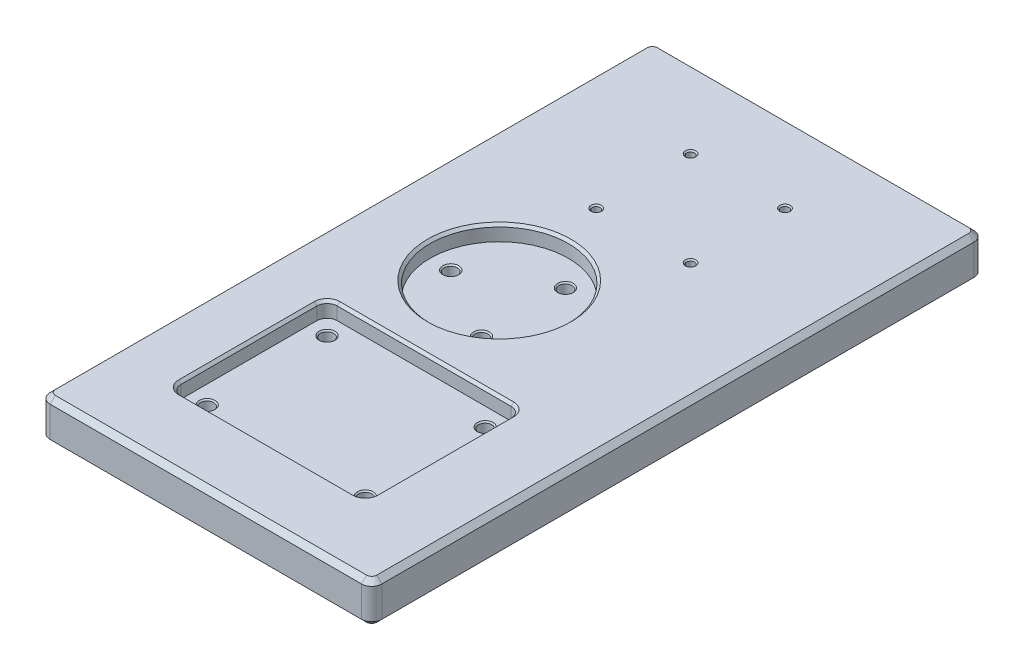
SolidWorks part; units mm, degrees
material "PET"
ref_plane "Front Plane" through (0, 0, 0) normal (0, 0, 1) x (1, 0, 0)
ref_plane "Top Plane" through (0, 0, 0) normal (0, 1, 0) x (1, 0, 0)
ref_plane "Right Plane" through (0, 0, 0) normal (1, 0, 0) x (0, 0, -1)
sketch "Sketch1" plane through (0, 0, 0) normal (0, 1, 0) x (1, 0, 0)
  line L1 (65, -120) -> (-65, -120)
  line L2 (65, -120) -> (65, 120)
  line L3 (65, 120) -> (-65, 120)
  line L4 (-65, -120) -> (-65, 120)
  line L5 (65, -120) -> (-65, 120) construction
  line L6 (65, 120) -> (-65, -120) construction
  point P0 (0, 0)
  dimension "D1" = 240
  dimension "D2" = 130
extrude "Boss-Extrude1" add sketch "Sketch1" along normal blind 16
sketch "Sketch7" plane through (0, 16, 0) normal (0, 1, 0) x (1, 0, 0)
  line L0 (-3, 0) -> (0, 0) construction
  line L1 (-41.1, -92.6) -> (35.1, -92.6)
  line L2 (-41.1, -92.6) -> (-41.1, -31.4)
  line L3 (-41.1, -31.4) -> (35.1, -31.4)
  line L4 (35.1, -92.6) -> (35.1, -31.4)
  line L5 (-41.1, -92.6) -> (35.1, -31.4) construction
  line L6 (-41.1, -31.4) -> (35.1, -92.6) construction
  line L7 (-3, 0) -> (-3, -62) construction
  point P0 (-3, -62)
  dimension "D1" = 76.2
  dimension "D2" = 61.2
  dimension "D3" = 3
  dimension "D4" = 62
extrude "Cut-Extrude5" cut sketch "Sketch7" against normal blind 6
sketch "Sketch2" plane through (0, 10, 0) normal (0, 1, 0) x (1, 0, 0)
  line L0 (-3, -31.4) -> (-3, -38.5) construction
  line L1 (28, -38.5) -> (-34, -38.5) construction
  line L2 (28, -38.5) -> (28, -85.5) construction
  line L3 (28, -85.5) -> (-34, -85.5) construction
  line L4 (-34, -38.5) -> (-34, -85.5) construction
  line L5 (28, -38.5) -> (-34, -85.5) construction
  line L6 (28, -85.5) -> (-34, -38.5) construction
  line L7 (-34, -62) -> (-41.1, -62) construction
  line L9 (35.1, -31.4) -> (-41.1, -31.4) construction
  line L10 (28, -62) -> (35.1, -62) construction
  line L11 (35.1, -92.6) -> (35.1, -31.4) construction
  line L12 (-3, -85.5) -> (-3, -92.6) construction
  line L13 (-41.1, -92.6) -> (35.1, -92.6) construction
  line L14 (-41.1, -31.4) -> (-41.1, -92.6) construction
  circle A0 centre (-34, -85.5) radius 2.6
  circle A1 centre (-34, -38.5) radius 2.6
  circle A2 centre (28, -38.5) radius 2.6
  circle A3 centre (28, -85.5) radius 2.6
  point P0 (-3, -62)
  dimension "D3" = 5.2
  dimension "D1" = 62
  dimension "D2" = 47
extrude "Cut-Extrude1" cut sketch "Sketch2" against normal through all
sketch "Sketch8" plane through (0, 16, 0) normal (0, 1, 0) x (1, 0, 0)
  line L0 (0, 0) -> (-13, 0) construction
  line L1 (-13, 0) -> (-13, 8) construction
  circle A0 centre (-13, 8) radius 27.1
  dimension "D1" = 54.2
  dimension "D2" = 8
  dimension "D3" = 13
extrude "Cut-Extrude6" cut sketch "Sketch8" against normal blind 6
sketch "Sketch9" plane through (0, 10, 0) normal (0, 1, 0) x (1, 0, 0)
  line L0 (-32, 8) -> (-13, 8) construction
  line L1 (-32, 8) -> (-3.5, 24.4545) construction
  line L2 (-3.5, 24.4545) -> (-3.5, -8.4545) construction
  line L3 (-3.5, -8.4545) -> (-32, 8) construction
  circle A0 centre (-13, 8) radius 19 construction
  circle A1 centre (-13, 8) radius 27.1 construction
  circle A2 centre (-32, 8) radius 2.6
  circle A3 centre (-3.5, 24.4545) radius 2.6
  circle A4 centre (-3.5, -8.4545) radius 2.6
  point P13 (-13, 8)
  dimension "D2" = 38
  dimension "D3" = 5.2
  dimension "D1" = 3
extrude "Cut-Extrude7" cut sketch "Sketch9" against normal through all
sketch "Sketch5" plane through (0, 16, 0) normal (0, 1, 0) x (1, 0, 0)
  line L0 (0, 70) -> (0, 0) construction
  line L1 (18.5, 88.5) -> (-18.5, 88.5) construction
  line L2 (18.5, 88.5) -> (18.5, 51.5) construction
  line L3 (18.5, 51.5) -> (-18.5, 51.5) construction
  line L4 (-18.5, 88.5) -> (-18.5, 51.5) construction
  line L5 (18.5, 88.5) -> (-18.5, 51.5) construction
  line L6 (18.5, 51.5) -> (-18.5, 88.5) construction
  circle A0 centre (-18.5, 51.5) radius 1.55
  circle A1 centre (-18.5, 88.5) radius 1.55
  circle A2 centre (18.5, 88.5) radius 1.55
  circle A3 centre (18.5, 51.5) radius 1.55
  point P0 (0, 70)
  dimension "D3" = 3.1
  dimension "D1" = 37
  dimension "D2" = 70
extrude "Cut-Extrude3" cut sketch "Sketch5" against normal through all
sketch "Sketch4" plane through (0, 0, 0) normal (0, -1, 0) x (1, 0, 0)
  circle A0 centre (-34, 85.5) radius 10
  circle A1 centre (28, 85.5) radius 10
  circle A2 centre (28, 38.5) radius 10
  circle A3 centre (-34, 38.5) radius 10
  circle A4 centre (-32, -8) radius 10
  circle A5 centre (-3.5, 8.4545) radius 10
  circle A6 centre (-3.5, -24.4545) radius 10
  circle A7 centre (-18.5, -51.5) radius 10
  circle A8 centre (-18.5, -88.5) radius 10
  circle A9 centre (18.5, -88.5) radius 10
  circle A10 centre (18.5, -51.5) radius 10
  dimension "D1" = 20
extrude "Cut-Extrude2" cut sketch "Sketch4" against normal offset from surface (5 mm away) 5 up to face at (28, 10, 88.1)
sketch "Sketch11" plane through (0, 5, 0) normal (0, -1, 0) x (1, 0, 0)
  circle A0 centre (18.5, -88.5) radius 10 construction
  circle A1 centre (-18.5, -88.5) radius 10 construction
  circle A2 centre (-18.5, -51.5) radius 10 construction
  circle A3 centre (18.5, -51.5) radius 10 construction
  circle A4 centre (18.5, -88.5) radius 10
  circle A5 centre (-18.5, -88.5) radius 10
  circle A6 centre (-18.5, -51.5) radius 10
  circle A7 centre (18.5, -51.5) radius 10
extrude "Cut-Extrude8" cut sketch "Sketch11" against normal offset from surface (6 mm away) 5 up to face at (18.5, 16, -49.95)
fillet "Fillet1" radius 4 8 edges at (35.1, 13, 31.4) (35.1, 13, 92.6) (-41.1, 13, 92.6) (-41.1, 13, 31.4) (-65, 8, -120) (65, 8, -120) (-65, 8, 120) (65, 8, 120)
chamfer "Chamfer3" distance 2 angle 45 16 edges at (0, 16, -120) (0, 0, -120) (-65, 16, 0) (-65, 0, 0) (0, 16, 120) (0, 0, 120) (65, 16, 0) (65, 0, 0) (-63.8284, 16, 118.8284) (-63.8284, 16, -118.8284) (63.8284, 16, 118.8284) (63.8284, 16, -118.8284) (-63.8284, 0, 118.8284) (-63.8284, 0, -118.8284) (63.8284, 0, 118.8284) (63.8284, 0, -118.8284)
chamfer "Chamfer1" distance 1 angle 45 20 edges at (28, 0, 28.5) (-34, 0, 28.5) (-34, 0, 75.5) (28, 0, 75.5) (35.1, 16, 62) (-3, 16, 92.6) (-41.1, 16, 62) (-3, 16, 31.4) (-32, 0, -18) (-3.5, 0, -34.4545) (-3.5, 0, -1.5455) (-13, 16, 19.1) (-18.5, 0, -61.5) (-18.5, 0, -98.5) (18.5, 0, -98.5) (18.5, 0, -61.5) (33.9284, 16, 91.4284) (-39.9284, 16, 91.4284) (33.9284, 16, 32.5716) (-39.9284, 16, 32.5716)
chamfer "Chamfer2" distance 0.5 angle 45 22 edges at (-34, 5, 82.9) (-34, 5, 35.9) (28, 5, 35.9) (28, 5, 82.9) (-18.5, 16, -86.95) (18.5, 16, -86.95) (18.5, 16, -49.95) (-18.5, 16, -49.95) (28, 10, 41.1) (28, 10, 88.1) (-34, 10, 88.1) (-34, 10, 41.1) (-3.5, 5, -27.0545) (-3.5, 5, 5.8545) (-32, 5, -10.6) (-32, 10, -5.4) (-3.5, 10, 11.0545) (-3.5, 10, -21.8545) (18.5, 11, -86.95) (-18.5, 11, -86.95) (-18.5, 11, -49.95) (18.5, 11, -49.95)
